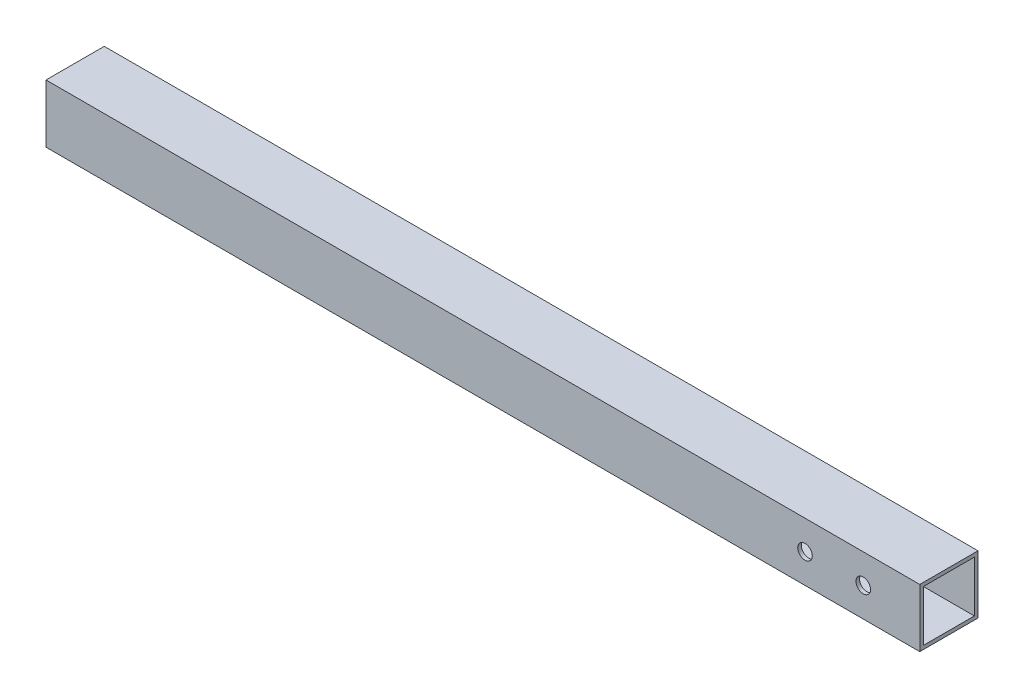
SolidWorks part; units mm, degrees
ref_plane "Front Plane" through (0, 0, 0) normal (0, 0, 1) x (1, 0, 0)
ref_plane "Top Plane" through (0, 0, 0) normal (0, 1, 0) x (1, 0, 0)
ref_plane "Right Plane" through (0, 0, 0) normal (1, 0, 0) x (0, 0, -1)
sketch "Sketch1" plane through (0, 0, 0) normal (1, 0, 0) x (0, 0, -1)
  line L0 (-11.1125, 11.1125) -> (-11.1125, -11.1125)
  line L1 (-12.7, 12.7) -> (12.7, 12.7)
  line L2 (-12.7, 12.7) -> (-12.7, -12.7)
  line L3 (-12.7, -12.7) -> (12.7, -12.7)
  line L4 (12.7, 12.7) -> (12.7, -12.7)
  line L5 (-12.7, 12.7) -> (12.7, -12.7) construction
  line L6 (-12.7, -12.7) -> (12.7, 12.7) construction
  line L7 (-11.1125, -11.1125) -> (11.1125, -11.1125)
  line L8 (11.1125, 11.1125) -> (11.1125, -11.1125)
  line L9 (-11.1125, 11.1125) -> (11.1125, 11.1125)
  point P0 (0, 0)
  dimension "D1" = 25.4
  dimension "D2" = 25.4
  dimension "D3" = 1.5875
extrude "Boss-Extrude1" add sketch "Sketch1" along normal blind 381
sketch "Sketch2" plane through (0, 0, -12.7) normal (0, 0, -1) x (-1, 0, 0)
  line L0 (-381, -12.7) -> (-381, 12.7) construction
  line L1 (-381, 12.7) -> (0, 12.7) construction
  circle A0 centre (-356.362, 0) radius 3.175
  circle A1 centre (-330.962, 0) radius 3.175
  dimension "D1" = 25.4
  dimension "D3" = 6.35
  dimension "D2" = 24.638
  dimension "D4" = 12.7
extrude "Cut-Extrude1" cut sketch "Sketch2" against normal blind 381
